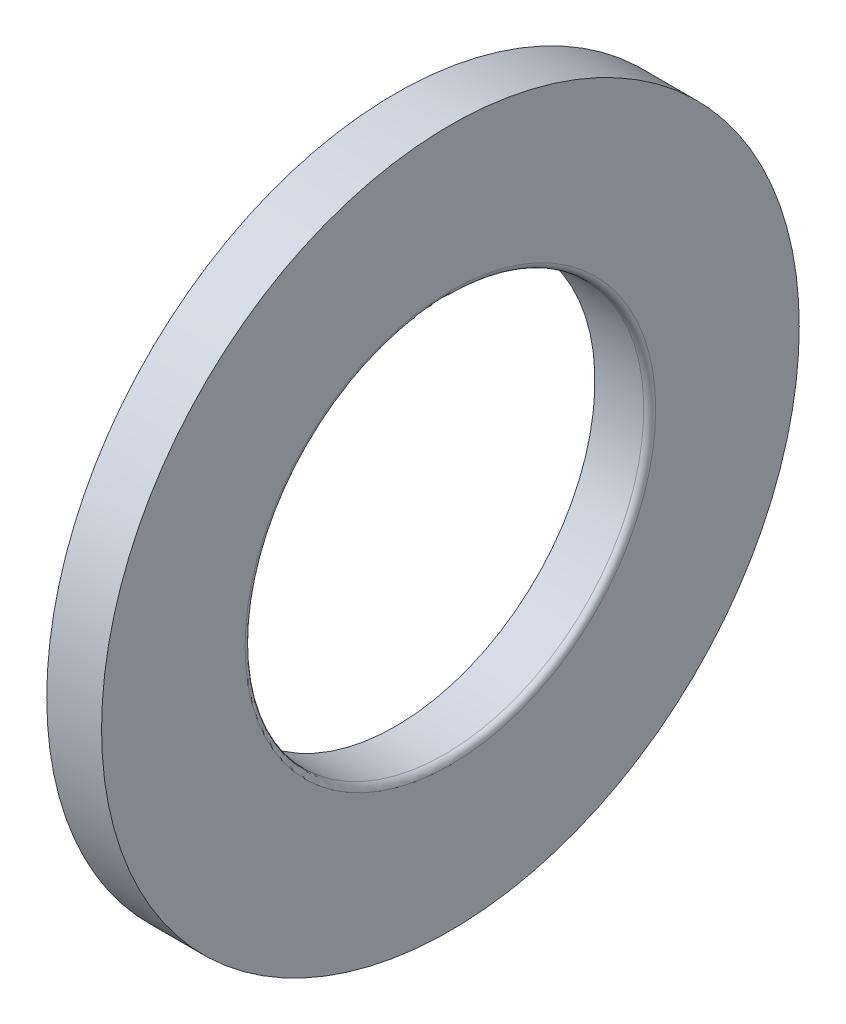
SolidWorks part; units mm, degrees
ref_plane "Front Plane" through (0, 0, 0) normal (0, 0, 1) x (1, 0, 0)
ref_plane "Top Plane" through (0, 0, 0) normal (0, 1, 0) x (1, 0, 0)
ref_plane "Right Plane" through (0, 0, 0) normal (1, 0, 0) x (0, 0, -1)
ref_plane "Plane1" through (0, 0, 0) normal (0, 0, 1) x (1, 0, 0)
sketch "Sketch1" plane through (0, 0, 0) normal (0, 0, 1) x (1, 0, 0)
  line L0 (1, 10) -> (3.45, 10)
  line L1 (3.75, 10.3) -> (3.75, 17.5)
  line L2 (3.75, 17.5) -> (1, 17.5)
  line L3 (1, 17.5) -> (1, 10)
  line L4 (50, 0) -> (-50, 0) construction
  arc A0 (3.45, 10) -> (3.75, 10.3) centre (3.45, 10.3) ccw
revolve "Revolve1" add sketch "Sketch1" angle 360 about L4
